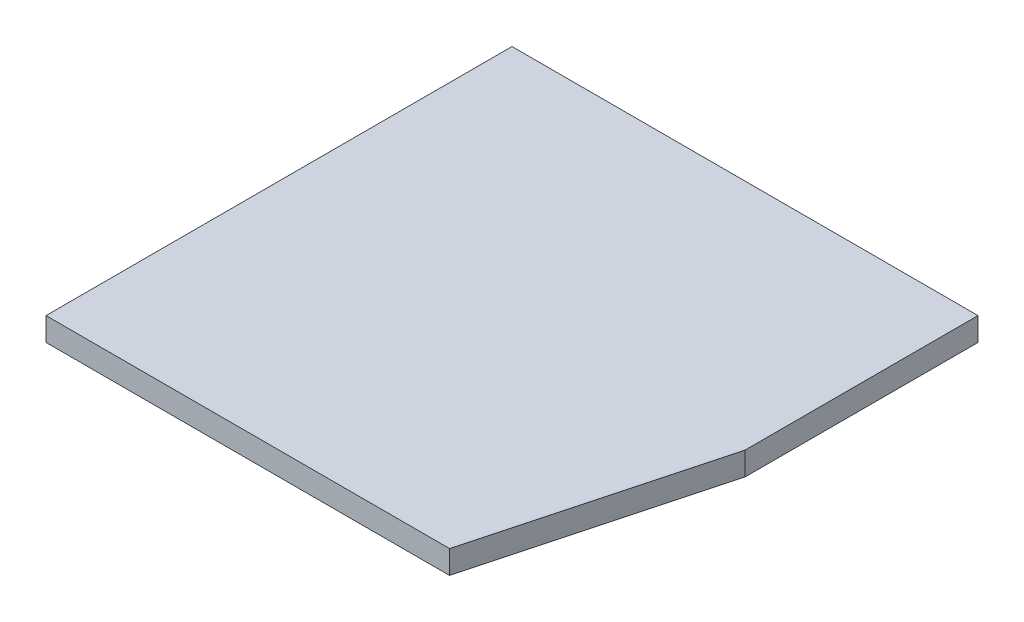
SolidWorks part; units mm, degrees
ref_plane "Front Plane" through (0, 0, 0) normal (0, 0, 1) x (1, 0, 0)
ref_plane "Top Plane" through (0, 0, 0) normal (0, 1, 0) x (1, 0, 0)
ref_plane "Right Plane" through (0, 0, 0) normal (1, 0, 0) x (0, 0, -1)
sketch "Sketch1" plane through (0, 0, 0) normal (0, 0, 1) x (1, 0, 0)
  line L1 (-63.5, -3.175) -> (63.5, -3.175)
  line L2 (-63.5, -3.175) -> (-63.5, 3.175)
  line L3 (-63.5, 3.175) -> (63.5, 3.175)
  line L4 (63.5, -3.175) -> (63.5, 3.175)
  line L5 (-63.5, -3.175) -> (63.5, 3.175) construction
  line L6 (-63.5, 3.175) -> (63.5, -3.175) construction
  point P0 (0, 0)
  dimension "D1" = 127
  dimension "D2" = 6.35
extrude "Boss-Extrude1" add sketch "Sketch1" along normal blind 127 contours L3 L4 L1 L2
sketch "Sketch2" plane through (0, -3.175, 0) normal (0, -1, 0) x (1, 0, 0)
  line L0 (63.5, 63.5) -> (46.4852, 127)
  line L1 (63.5, 127) -> (63.5, 0) construction
  line L2 (-63.5, 127) -> (63.5, 127) construction
  line L3 (46.4852, 127) -> (63.5, 127)
  line L4 (63.5, 127) -> (63.5, 63.5)
  dimension "D1" = 15
extrude "Cut-Extrude1" cut sketch "Sketch2" against normal through all and the other way through all contours L3 L4 L0
